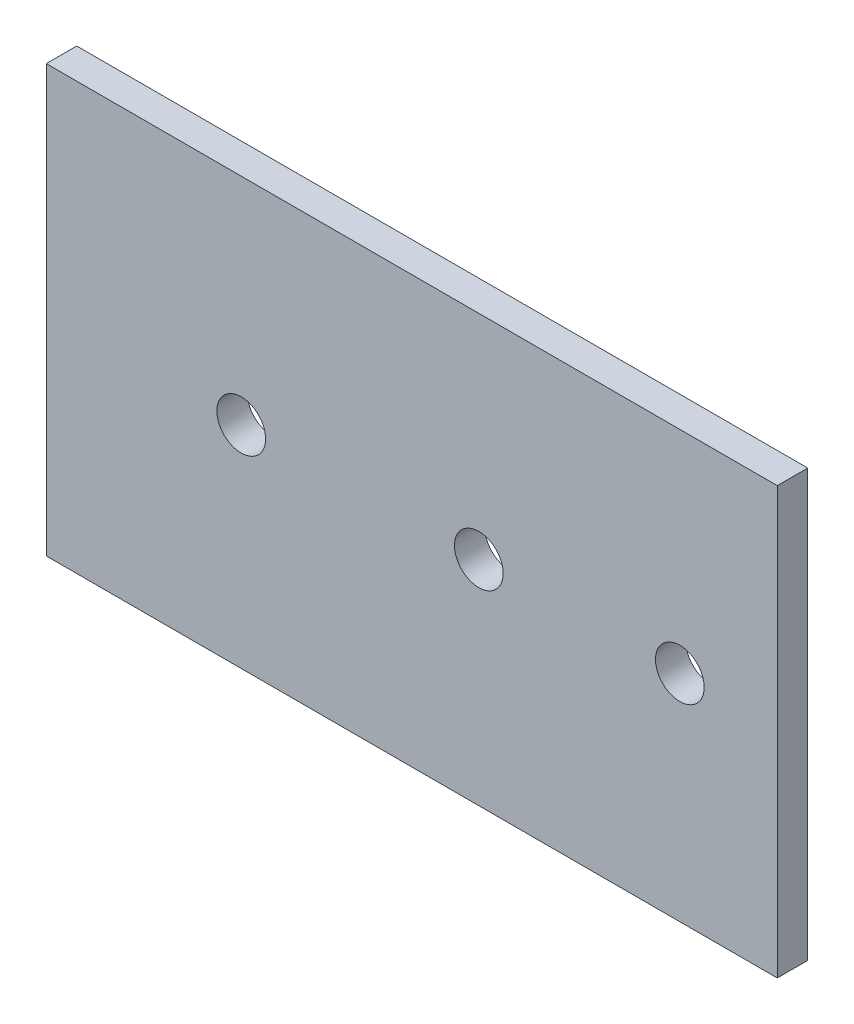
SolidWorks part; units mm, degrees
ref_plane "Front Plane" through (0, 0, 0) normal (0, 0, 1) x (1, 0, 0)
ref_plane "Top Plane" through (0, 0, 0) normal (0, 1, 0) x (1, 0, 0)
ref_plane "Right Plane" through (0, 0, 0) normal (1, 0, 0) x (0, 0, -1)
sketch "Sketch1" plane through (0, 0, 0) normal (0, 0, 1) x (1, 0, 0)
  line L1 (-75, -35) -> (75, -35)
  line L2 (-75, -35) -> (-75, 35)
  line L3 (-75, 35) -> (75, 35)
  line L4 (75, -35) -> (75, 35)
  line L5 (-75, -35) -> (75, 35) construction
  line L6 (-75, 35) -> (75, -35) construction
  point P0 (0, 0)
  dimension "D1" = 150
  dimension "D2" = 70
extrude "Boss-Extrude1" add sketch "Sketch1" along normal mid plane 5
sketch "Sketch2" plane through (0, 0, 2.5) normal (0, 0, 1) x (1, 0, 0)
  circle A0 centre (63, 0.6285) radius 4
  circle A1 centre (29.0015, 0.3096) radius 4
  circle A2 centre (-42.9953, -0.3659) radius 4
  circle A3 centre (-3.9971, 0) radius 4
  dimension "D1" = 8
  dimension "D2" = 8
  dimension "D3" = 8
  dimension "D4" = 8
extrude "Cut-Extrude1" cut sketch "Sketch2" against normal through all
sketch "Sketch3" plane through (0, 0, 2.5) normal (0, 0, 1) x (1, 0, 0)
  line L0 (75, 35) -> (-75, 35) construction
  line L1 (75, -35) -> (45, -35)
  line L2 (75, -35) -> (75, 35)
  line L3 (75, 35) -> (45, 35)
  line L4 (45, -35) -> (45, 35)
  dimension "D1" = 30
extrude "Cut-Extrude2" cut sketch "Sketch3" against normal through all
